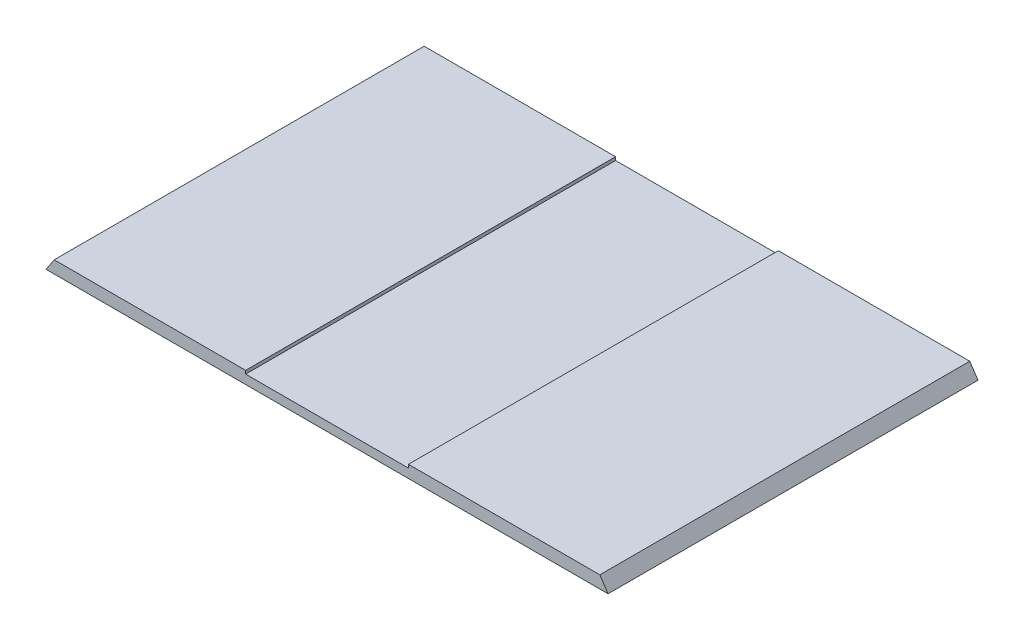
SolidWorks part; units mm, degrees
ref_plane "Ebene vorne" through (0, 0, 0) normal (0, 0, 1) x (1, 0, 0)
ref_plane "Ebene oben" through (0, 0, 0) normal (0, 1, 0) x (1, 0, 0)
ref_plane "Ebene rechts" through (0, 0, 0) normal (1, 0, 0) x (0, 0, -1)
sketch "Skizze1" plane through (0, 0, 0) normal (0, 0, 1) x (1, 0, 0)
  line L0 (331.8583, -179.3676) -> (341.8583, -194.3676)
  line L1 (-331.8583, -179.3676) -> (-341.8583, -194.3676)
  line L2 (341.8583, -194.3676) -> (-341.8583, -194.3676)
  line L19 (-99, -179.3676) -> (-331.8583, -179.3676)
  line L26 (-99, -179.3676) -> (-99, -183.3676)
  line L27 (-99, -183.3676) -> (99, -183.3676)
  line L40 (99, -179.3676) -> (331.8583, -179.3676)
  line L41 (99, -179.3676) -> (99, -183.3676)
extrude "Aufsatz-Linear austragen1" add sketch "Skizze1" along normal blind 450
